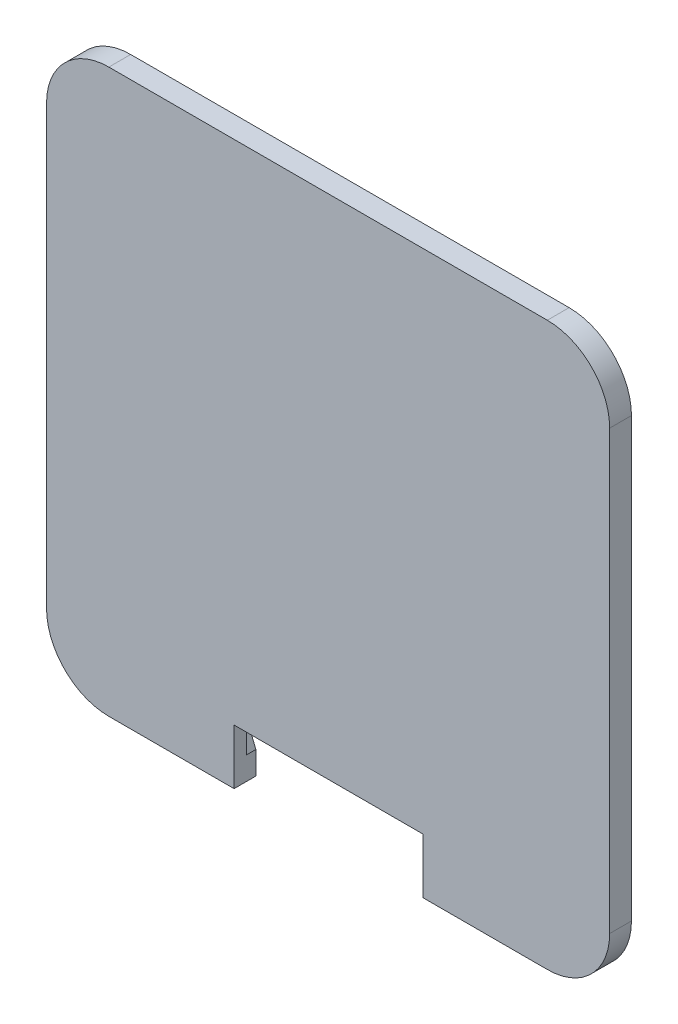
SolidWorks part; units mm, degrees
material "PET"
ref_plane "Front Plane" through (0, 0, 0) normal (0, 0, 1) x (1, 0, 0)
ref_plane "Top Plane" through (0, 0, 0) normal (0, 1, 0) x (1, 0, 0)
ref_plane "Right Plane" through (0, 0, 0) normal (1, 0, 0) x (0, 0, -1)
sketch "Sketch1" plane through (0, 0, 0) normal (0, 0, 1) x (1, 0, 0)
  line L8 (-50.8502, -30.122) -> (-45.1855, -30.122)
  line L9 (15.2147, -41.425) -> (15.2147, -45.122)
  line L10 (-35.1855, -45.122) -> (35.1855, -45.122)
  line L11 (-45.1855, -35.122) -> (-45.1855, 35.122)
  line L12 (-35.1855, 45.122) -> (35.1855, 45.122)
  line L13 (45.1855, -35.122) -> (45.1855, 35.122)
  line L14 (-45.1855, -45.122) -> (45.1855, 45.122) construction
  line L15 (-45.1855, 45.122) -> (45.1855, -45.122) construction
  line L16 (-30.1855, 24.892) -> (-30.1855, -24.892)
  line L17 (-24.9555, -30.122) -> (-19.7221, -30.122)
  line L18 (-19.7221, -30.122) -> (-15.0866, -41.425)
  line L19 (-15.0866, -41.425) -> (15.2147, -41.425)
  line L20 (15.2147, -41.425) -> (19.7232, -30.122)
  line L21 (19.7232, -30.122) -> (24.9555, -30.122)
  line L22 (30.1855, -24.892) -> (30.1855, 24.892)
  line L23 (24.9555, 30.122) -> (-24.9555, 30.122)
  line L24 (-30.1855, 24.892) -> (-30.1855, -24.892)
  line L25 (-24.9555, -30.122) -> (-19.7221, -30.122)
  line L26 (-19.7221, -30.122) -> (-15.0866, -41.425)
  line L27 (-15.0866, -41.425) -> (15.2147, -41.425)
  line L28 (15.2147, -41.425) -> (19.7232, -30.122)
  line L29 (19.7232, -30.122) -> (24.9555, -30.122)
  line L30 (30.1855, -24.892) -> (30.1855, 24.892)
  line L31 (24.9555, 30.122) -> (-24.9555, 30.122)
  line L32 (-15.0866, -41.425) -> (-15.0866, -45.122)
  line L33 (19.7232, -30.122) -> (24.9555, -30.122)
  line L34 (45.1855, -30.122) -> (50.8502, -30.122)
  line L35 (-24.9555, -30.122) -> (-19.7221, -30.122)
  arc A4 (35.1855, -45.122) -> (45.1855, -35.122) centre (35.1855, -35.122) ccw
  arc A5 (-35.1855, -45.122) -> (-45.1855, -35.122) centre (-35.1855, -35.122) cw
  arc A6 (-45.1855, 35.122) -> (-35.1855, 45.122) centre (-35.1855, 35.122) cw
  arc A7 (35.1855, 45.122) -> (45.1855, 35.122) centre (35.1855, 35.122) cw
  arc A8 (-24.9555, 30.122) -> (-30.1855, 24.892) centre (-24.9555, 24.892) ccw
  arc A9 (-30.1855, -24.892) -> (-24.9555, -30.122) centre (-24.9555, -24.892) ccw
  arc A10 (24.9555, -30.122) -> (30.1855, -24.892) centre (24.9555, -24.892) ccw
  arc A11 (30.1855, 24.892) -> (24.9555, 30.122) centre (24.9555, 24.892) ccw
  arc A12 (-24.9555, 30.122) -> (-30.1855, 24.892) centre (-24.9555, 24.892) ccw
  arc A13 (-30.1855, -24.892) -> (-24.9555, -30.122) centre (-24.9555, -24.892) ccw
  arc A14 (24.9555, -30.122) -> (30.1855, -24.892) centre (24.9555, -24.892) ccw
  arc A15 (30.1855, 24.892) -> (24.9555, 30.122) centre (24.9555, 24.892) ccw
  point P0 (0, 0)
  point P3 (0, -30.122)
  dimension "D4" = 10
  dimension "D2" = 15
  dimension "D3" = 15
  dimension "D1" = 0.15
extrude "Boss-Extrude1" add sketch "Sketch1" against normal blind 1.5 contours A15 L30 A14 L29 L28 L9 L10 A4 L13 A7 L12 A6 L11 A5 L32 L26 L25 A13 L24 A12 L31
sketch "Sketch2" plane through (0, 0, 0) normal (0, 0, 1) x (1, 0, 0)
  line L0 (-45.1855, -35.122) -> (-45.1855, 35.122) construction
  line L1 (-35.1855, -45.122) -> (35.1855, -45.122)
  line L2 (-45.1855, -35.122) -> (-45.1855, 35.122)
  line L3 (-35.1855, 45.122) -> (35.1855, 45.122)
  line L4 (45.1855, -35.122) -> (45.1855, 35.122)
  line L5 (-45.1855, -45.122) -> (45.1855, 45.122) construction
  line L6 (-45.1855, 45.122) -> (45.1855, -45.122) construction
  line L7 (-35.1855, -45.122) -> (-15.0866, -45.122) construction
  line L8 (-14.986, -41.275) -> (15.113, -41.275) construction
  line L9 (-15.0866, -45.122) -> (15.2147, -45.122)
  line L10 (-15.0866, -45.122) -> (-15.0866, -36.275)
  line L11 (-15.0866, -36.275) -> (15.2147, -36.275)
  line L12 (15.2147, -45.122) -> (15.2147, -36.275)
  arc A0 (35.1855, -45.122) -> (45.1855, -35.122) centre (35.1855, -35.122) ccw
  arc A1 (-35.1855, -45.122) -> (-45.1855, -35.122) centre (-35.1855, -35.122) cw
  arc A2 (-45.1855, 35.122) -> (-35.1855, 45.122) centre (-35.1855, 35.122) cw
  arc A3 (35.1855, 45.122) -> (45.1855, 35.122) centre (35.1855, 35.122) cw
  point P0 (0, 0)
  arc M9 (24.9555, 30.122) -> (30.1855, 24.892) centre (24.9555, 24.892) cw
  line M10 (30.1855, 24.892) -> (30.1855, -24.892)
  arc M11 (30.1855, -24.892) -> (24.9555, -30.122) centre (24.9555, -24.892) cw
  line M12 (24.9555, -30.122) -> (19.7232, -30.122)
  line M13 (19.7232, -30.122) -> (15.2147, -41.425)
  line M14 (15.2147, -41.425) -> (15.2147, -45.122)
  line M15 (15.2147, -45.122) -> (35.1855, -45.122)
  arc M16 (35.1855, -45.122) -> (45.1855, -35.122) centre (35.1855, -35.122) ccw
  line M17 (45.1855, -35.122) -> (45.1855, 35.122)
  arc M18 (45.1855, 35.122) -> (35.1855, 45.122) centre (35.1855, 35.122) ccw
  line M19 (35.1855, 45.122) -> (-35.1855, 45.122)
  arc M20 (-35.1855, 45.122) -> (-45.1855, 35.122) centre (-35.1855, 35.122) ccw
  line M21 (-45.1855, 35.122) -> (-45.1855, -35.122)
  arc M22 (-45.1855, -35.122) -> (-35.1855, -45.122) centre (-35.1855, -35.122) ccw
  line M23 (-35.1855, -45.122) -> (-15.0866, -45.122)
  line M24 (-15.0866, -45.122) -> (-15.0866, -41.425)
  line M25 (-15.0866, -41.425) -> (-19.7221, -30.122)
  line M26 (-19.7221, -30.122) -> (-24.9555, -30.122)
  arc M27 (-24.9555, -30.122) -> (-30.1855, -24.892) centre (-24.9555, -24.892) cw
  line M28 (-30.1855, -24.892) -> (-30.1855, 24.892)
  arc M29 (-30.1855, 24.892) -> (-24.9555, 30.122) centre (-24.9555, 24.892) cw
  line M30 (-24.9555, 30.122) -> (24.9555, 30.122)
  dimension "D3" = 10
  dimension "D1" = 0
  dimension "D2" = 0
  dimension "D4" = 5
extrude "Boss-Extrude2" add sketch "Sketch2" along normal blind 2 contours M30 M9 M10 M11 M12 M13 M14 M15 M16 M17 M18 M19 M20 M21 M22 M23 M24 M25 M26 M27 M28 M29 | L12 L10 L11 M13 M12 M11 M10 M9 M30 M29 M28 M27 M26 M25
